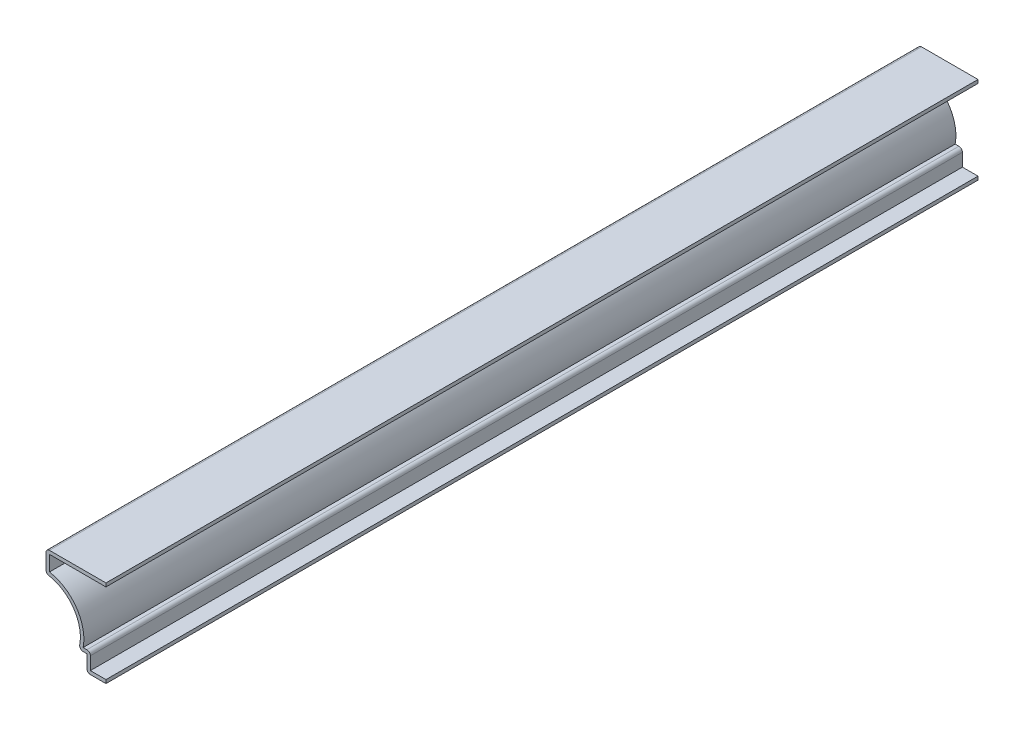
SolidWorks part; units mm, degrees
ref_plane "Front Plane" through (0, 0, 0) normal (0, 0, 1) x (1, 0, 0)
ref_plane "Top Plane" through (0, 0, 0) normal (0, 1, 0) x (1, 0, 0)
ref_plane "Right Plane" through (0, 0, 0) normal (1, 0, 0) x (0, 0, -1)
sketch "Sketch1" plane through (0, 0, 0) normal (0, 0, 1) x (1, 0, 0)
  line L0 (0, 0) -> (-5.5562, 0)
  line L1 (-5.5562, 0) -> (-5.5562, 4.7625)
  line L2 (-5.5562, 4.7625) -> (-7.9375, 4.7625)
  line L3 (-17.4625, 19.05) -> (-17.4625, 25.4)
  line L4 (-17.4625, 25.4) -> (0, 25.4)
  arc A0 (-7.9375, 4.7625) -> (-17.4625, 19.05) centre (-18.5701, 7.9928) ccw
  point P7 (0, 0)
  dimension "D6" = 11.1125
  dimension "D1" = 5.5562
  dimension "D2" = 25.4
  dimension "D3" = 17.4625
  dimension "D4" = 4.7625
  dimension "D5" = 2.3813
  dimension "D7" = 6.35
  dimension "D8" = 14.2875
  dimension "D9" = 9.525
extrude "Extrude-Thin1" add sketch "Sketch1" against normal blind 254 thin
fillet "Fillet1" radius 1.016 5 edges at (-5.5562, 0, -127) (-4.5402, 5.7785, -127) (-7.9375, 4.7625, -127) (-17.4625, 19.05, -127) (-17.4625, 25.4, -127)
